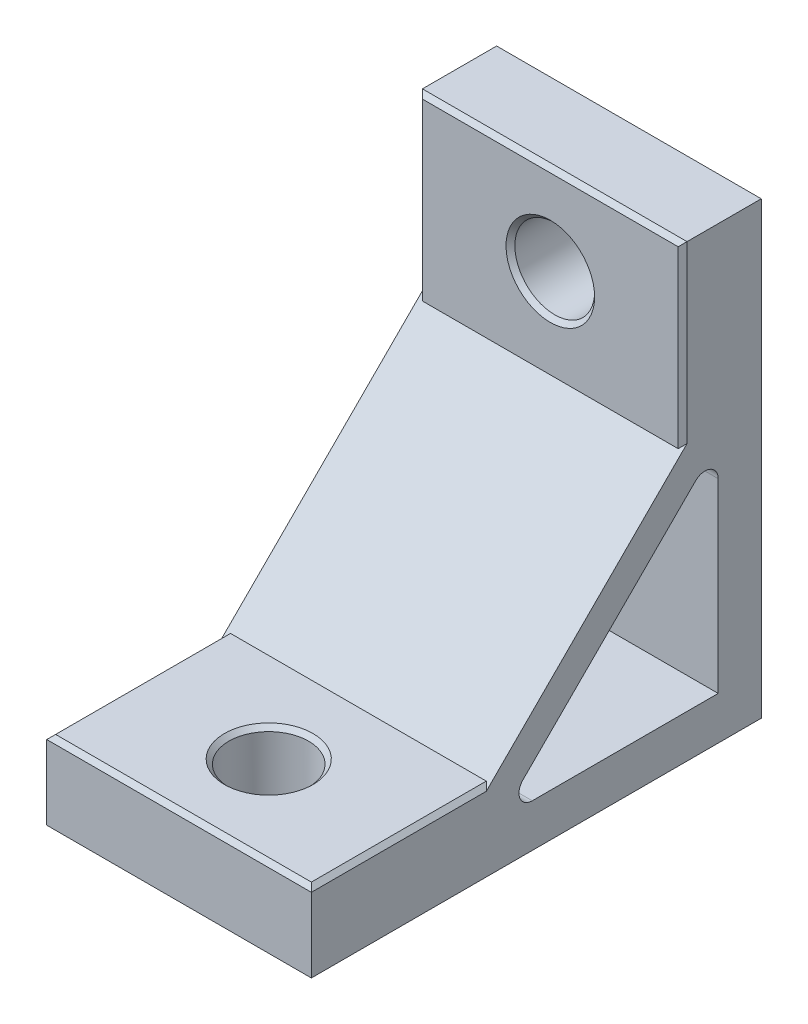
SolidWorks part; units mm, degrees
ref_plane "Front Plane" through (0, 0, 0) normal (0, 0, 1) x (1, 0, 0)
ref_plane "Top Plane" through (0, 0, 0) normal (0, 1, 0) x (1, 0, 0)
ref_plane "Right Plane" through (0, 0, 0) normal (1, 0, 0) x (0, 0, -1)
sketch "Sketch1" plane through (0, 0, 0) normal (1, 0, 0) x (0, 0, -1)
  line L0 (-21.67, 0) -> (-41.92, 0)
  line L1 (-41.92, 0) -> (-41.92, -8.88)
  line L2 (-41.92, -8.88) -> (8.88, -8.88)
  line L3 (8.88, -8.88) -> (8.88, 41.92)
  line L4 (8.88, 41.92) -> (0, 41.92)
  line L5 (0, 41.92) -> (0, 21.67)
  line L6 (-16.5788, 0) -> (0, 16.5788) construction
  line L7 (0, 21.67) -> (-21.67, 0)
  line L8 (0, 0) -> (-16.5788, 0) construction
  line L9 (0, 16.5788) -> (0, 0) construction
  line L10 (-16.5788, 0) -> (-21.67, 0) construction
  line L11 (0, 21.67) -> (0, 16.5788) construction
  dimension "D1" = 8.88
  dimension "D2" = 50.8
  dimension "D3" = 20.25
  dimension "D4" = 3.6
  dimension "D5" = 45
extrude "Boss-Extrude1" add sketch "Sketch1" along normal mid plane 29.88
sketch "Sketch2" plane through (0, 0, 0) normal (1, 0, 0) x (0, 0, -1)
  line L0 (-16.5788, 0) -> (0, 16.5788) construction
  line L1 (-20.5988, -4.02) -> (4.02, 20.5988)
  line L6 (-41.92, -8.88) -> (8.88, -8.88) construction
  line L7 (8.88, -8.88) -> (8.88, 41.92) construction
  line L8 (-20.5988, -4.02) -> (-41.92, -4.02) construction
  line L9 (-41.92, 0) -> (-41.92, -8.88) construction
  line L10 (4.02, -8.88) -> (4.02, 41.92) construction
  line L11 (8.88, 41.92) -> (0, 41.92) construction
  line L12 (-41.92, -8.88) -> (8.88, -8.88)
  line L13 (8.88, -8.88) -> (-10.835, 10.835) construction
  line L14 (0, 21.67) -> (-21.67, 0) construction
  line L15 (4.02, 20.5988) -> (4.02, -4.02)
  line L16 (-20.5988, -4.02) -> (4.02, -4.02)
  point P7 (0, 0)
  point P19 (0, 0)
  point P20 (4.02, -4.02)
  point P22 (-0.4242, 16.1546)
  point P23 (0, 0)
  dimension "D1" = 4.86
extrude "Cut-Extrude1" cut sketch "Sketch2" against normal through all both and the other way through all contours L1 L16 L15
fillet "Fillet1" radius 1.5 2 edges at (0, -4.02, 20.5988) (0, 20.5988, -4.02)
hole_wizard "Ø1.0mm Dowel Hole1" positions "Sketch3" profile "Sketch4" hole size "Ø1.0" standard "ANSI Metric" end condition through all
sketch "Sketch3" plane through (0, 0, 0) normal (0, 1, 0) x (1, 0, 0)
  line L0 (14.94, -41.92) -> (-14.94, -21.67) construction
  point P0 (0, -31.795)
  point P9 (0, 0)
sketch "Sketch4" plane through (0, 0, 31.795) normal (1, 0, 0) x (0, 0, 1)
  line L0 (0, 0) -> (0, 8.88)
  line L1 (0, 8.88) -> (4.5, 8.88)
  line L2 (4.5, 8.88) -> (4.5, 0)
  line L5 (4.5, 0) -> (0, 0)
  line L11 (0, -6.35) -> (0, 107.95) construction
  dimension "Thru Hole Dia." = 9
  dimension "Thru Hole Depth" = 8.88
hole_wizard "Ø1.0mm Dowel Hole2" positions "Sketch5" profile "Sketch6" hole size "Ø1.0" standard "ANSI Metric" end condition through all
sketch "Sketch5" plane through (0, 0, 0) normal (0, 0, 1) x (1, 0, 0)
  line L0 (14.94, 41.92) -> (-14.94, 21.67)
  point P7 (0, 31.795)
sketch "Sketch6" plane through (0, 31.795, 0) normal (1, 0, 0) x (0, -1, 0)
  line L0 (0, 0) -> (0, 8.88)
  line L1 (0, 8.88) -> (4.5, 8.88)
  line L2 (4.5, 8.88) -> (4.5, 0)
  line L5 (4.5, 0) -> (0, 0)
  line L11 (0, -6.35) -> (0, 107.95) construction
  dimension "Thru Hole Dia." = 9
  dimension "Thru Hole Depth" = 8.88
chamfer "Chamfer1" distance 0.5 angle 45 8 edges at (0, 0, 36.295) (14.94, 0, 31.795) (0, 0, 41.92) (-14.94, 0, 31.795) (4.5, 31.795, 0) (-14.94, 31.795, 0) (0, 41.92, 0) (14.94, 31.795, 0)
